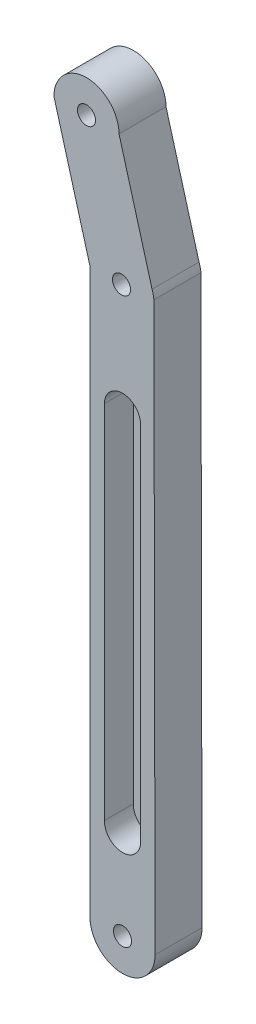
SolidWorks part; units mm, degrees
ref_plane "Front Plane" through (0, 0, 0) normal (0, 0, 1) x (1, 0, 0)
ref_plane "Top Plane" through (0, 0, 0) normal (0, 1, 0) x (1, 0, 0)
ref_plane "Right Plane" through (0, 0, 0) normal (1, 0, 0) x (0, 0, -1)
sketch "Sketch1" plane through (0, 0, 0) normal (0, 0, 1) x (1, 0, 0)
  line L0 (-11.1146, 113.2774) -> (-11.1146, -42.6363)
  line L1 (6.8854, -42.6363) -> (6.5651, 114.0728)
  line L4 (-11.1146, 113.2774) -> (-21.0849, 148.9873)
  line L5 (6.0537, 116.3662) -> (-3.0849, 148.9873)
  circle A0 centre (-2.3997, 113.2774) radius 2.5
  circle A1 centre (-2.1146, -42.6363) radius 2.5
  arc A2 (-11.1146, -42.6363) -> (6.8854, -42.6363) centre (-2.1146, -42.6363) ccw
  arc A3 (6.5651, 114.0728) -> (6.0537, 116.3662) centre (-2.3997, 113.2774) ccw
  circle A4 centre (-12.0849, 148.9873) radius 2.5
  arc A5 (-3.0849, 148.9873) -> (-21.0849, 148.9873) centre (-12.0849, 148.9873) ccw
  dimension "D2" = 18
  dimension "D3" = 18
  dimension "D4" = 5
  dimension "D5" = 5
  dimension "D8" = 5
  dimension "D1" = 155.914
  dimension "D7" = 37
extrude "Extrude1" add sketch "Sketch1" along normal blind 13
sketch "Sketch2" plane through (0, 0, 13) normal (0, 0, 1) x (1, 0, 0)
  line L0 (-11.1146, 113.2774) -> (-11.1146, -42.6363) construction
  line L1 (2.8854, 82.3637) -> (2.8286, -16.885)
  line L2 (-7.1146, 82.3637) -> (-7.1121, -17.4771)
  arc A0 (2.8854, 82.3637) -> (-7.1146, 82.3637) centre (-2.1146, 82.3637) ccw
  arc A1 (-7.1121, -17.4771) -> (2.8286, -16.885) centre (-2.1146, -17.6363) ccw
  circle A2 centre (-2.1146, -42.6363) radius 2.5 construction
  dimension "D1" = 10
  dimension "D2" = 10
  dimension "D3" = 9
  dimension "D4" = 9
  dimension "D5" = 100
  dimension "D6" = 25
extrude "Extrude2" cut sketch "Sketch2" against normal blind 8
